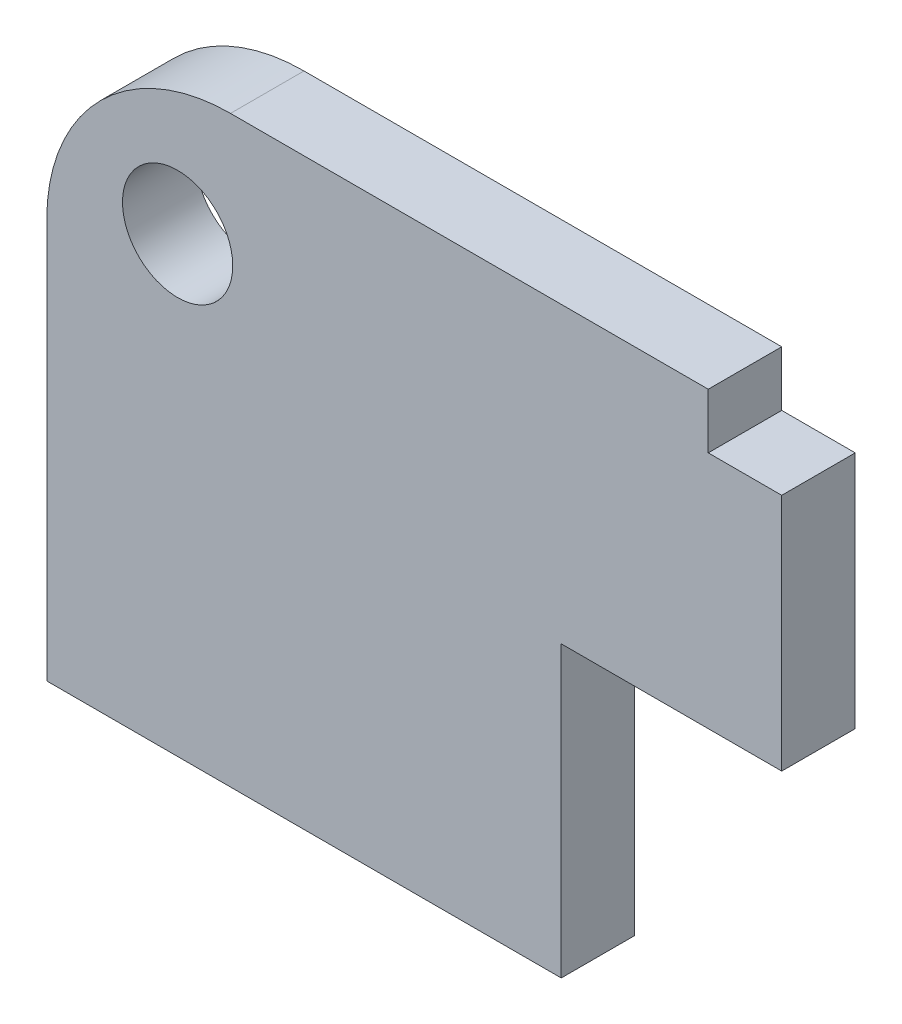
SolidWorks part; units mm, degrees
ref_plane "Front Plane" through (0, 0, 0) normal (0, 0, 1) x (1, 0, 0)
ref_plane "Top Plane" through (0, 0, 0) normal (0, 1, 0) x (1, 0, 0)
ref_plane "Right Plane" through (0, 0, 0) normal (1, 0, 0) x (0, 0, -1)
sketch "Sketch1" plane through (0, 0, 0) normal (0, 0, 1) x (1, 0, 0)
  line L0 (14, -8) -> (20, -8)
  line L7 (14, -15.8756) -> (0, -15.8756)
  line L8 (14, -15.8756) -> (14, -8)
  line L9 (20, -1.5) -> (20, -8)
  line L10 (5, 0) -> (18, 0)
  line L11 (18, -1.5) -> (18, 0)
  line L12 (20, -1.5) -> (18, -1.5)
  line L13 (0, -15.8756) -> (0, -5)
  arc A0 (0, -5) -> (5, 0) centre (5, -5) cw
  circle A1 centre (3.5607, -3.5607) radius 1.5
  point P2 (0, 0)
  dimension "D7" = 3.5607
  dimension "D8" = 8
  dimension "D1" = 3
  dimension "D2" = 5
  dimension "D3" = 3.5607
  dimension "D4" = 14
  dimension "D5" = 18
  dimension "D6" = 20
  dimension "D9" = 15.8756
extrude "Boss-Extrude1" add sketch "Sketch1" along normal blind 2
